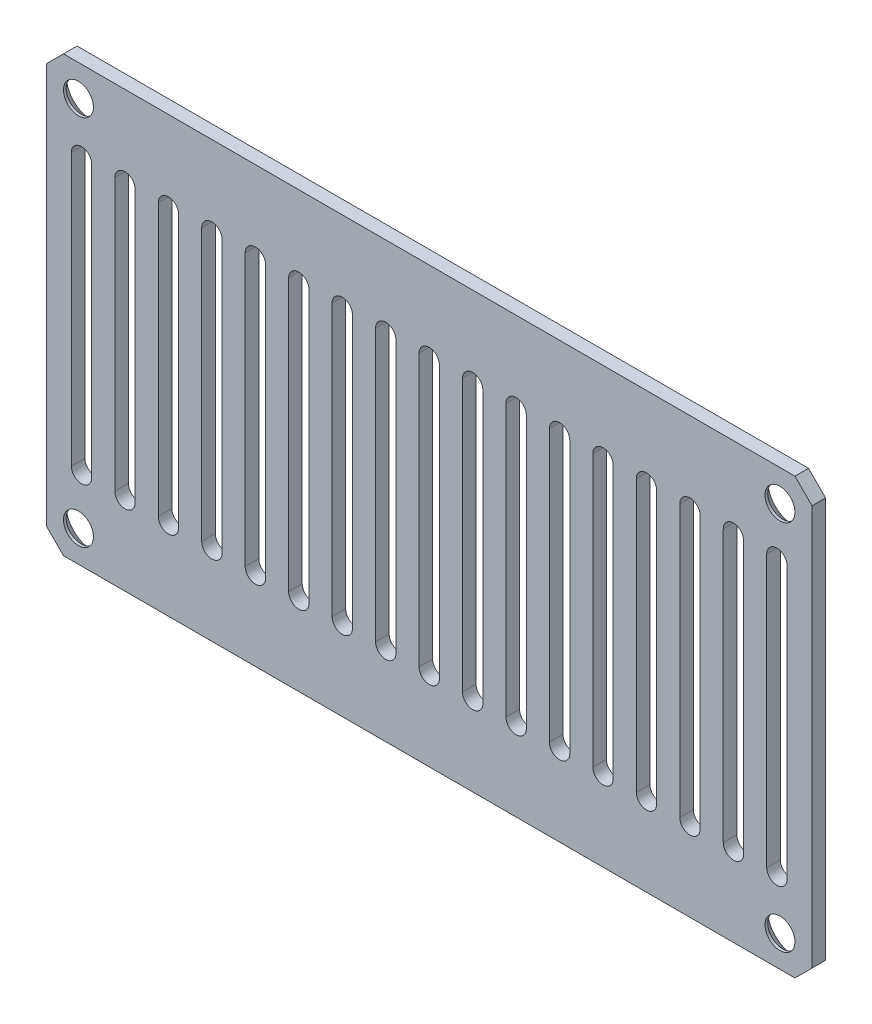
SolidWorks part; units mm, degrees
ref_plane "Front Plane" through (0, 0, 0) normal (0, 0, 1) x (1, 0, 0)
ref_plane "Top Plane" through (0, 0, 0) normal (0, 1, 0) x (1, 0, 0)
ref_plane "Right Plane" through (0, 0, 0) normal (1, 0, 0) x (0, 0, -1)
sketch "Sketch1" plane through (0, 0, 0) normal (0, 0, 1) x (1, 0, 0)
  line L1 (0, 0) -> (89.5, 0)
  line L2 (0, 0) -> (0, 50.8)
  line L3 (0, 50.8) -> (89.5, 50.8)
  line L4 (89.5, 0) -> (89.5, 50.8)
  dimension "D1" = 89.5
  dimension "D2" = 50.8
extrude "Boss-Extrude1" add sketch "Sketch1" along normal blind 1.5875
chamfer "Chamfer1" distance 2 angle 45 4 edges at (0, 0, 0.7937) (0, 50.8, 0.7937) (89.5, 0, 0.7937) (89.5, 50.8, 0.7937)
sketch "Sketch2" plane through (0, 0, 0) normal (0, 0, -1) x (-1, 0, 0)
  line L0 (-44.75, 50.8) -> (-44.75, 0) construction
  line L1 (-87.5, 50.8) -> (-2, 50.8) construction
  line L2 (-2, 0) -> (-87.5, 0) construction
  line L3 (-44.75, 41.275) -> (-44.75, 9.525) construction
  line L4 (-43.5594, 41.275) -> (-43.5594, 9.525)
  line L5 (-45.9406, 41.275) -> (-45.9406, 9.525)
  line L6 (-89.5, 25.4) -> (0, 25.4) construction
  line L7 (-89.5, 2) -> (-89.5, 48.8) construction
  line L8 (0, 48.8) -> (0, 2) construction
  line L9 (-39.67, 41.275) -> (-39.67, 9.525) construction
  line L10 (-38.4794, 41.275) -> (-38.4794, 9.525)
  line L11 (-40.8606, 41.275) -> (-40.8606, 9.525)
  line L12 (-34.59, 41.275) -> (-34.59, 9.525) construction
  line L13 (-33.3994, 41.275) -> (-33.3994, 9.525)
  line L14 (-35.7806, 41.275) -> (-35.7806, 9.525)
  line L15 (-29.51, 41.275) -> (-29.51, 9.525) construction
  line L16 (-28.3194, 41.275) -> (-28.3194, 9.525)
  line L17 (-30.7006, 41.275) -> (-30.7006, 9.525)
  line L18 (-24.43, 41.275) -> (-24.43, 9.525) construction
  line L19 (-23.2394, 41.275) -> (-23.2394, 9.525)
  line L20 (-25.6206, 41.275) -> (-25.6206, 9.525)
  line L21 (-19.35, 41.275) -> (-19.35, 9.525) construction
  line L22 (-18.1594, 41.275) -> (-18.1594, 9.525)
  line L23 (-20.5406, 41.275) -> (-20.5406, 9.525)
  line L24 (-14.27, 41.275) -> (-14.27, 9.525) construction
  line L25 (-13.0794, 41.275) -> (-13.0794, 9.525)
  line L26 (-15.4606, 41.275) -> (-15.4606, 9.525)
  line L27 (-9.19, 41.275) -> (-9.19, 9.525) construction
  line L28 (-7.9994, 41.275) -> (-7.9994, 9.525)
  line L29 (-10.3806, 41.275) -> (-10.3806, 9.525)
  line L30 (-4.11, 41.275) -> (-4.11, 9.525) construction
  line L31 (-2.9194, 41.275) -> (-2.9194, 9.525)
  line L32 (-5.3006, 41.275) -> (-5.3006, 9.525)
  line L33 (-49.83, 41.275) -> (-49.83, 9.525) construction
  line L34 (-48.6394, 41.275) -> (-48.6394, 9.525)
  line L35 (-51.0206, 41.275) -> (-51.0206, 9.525)
  line L36 (-54.91, 41.275) -> (-54.91, 9.525) construction
  line L37 (-53.7194, 41.275) -> (-53.7194, 9.525)
  line L38 (-56.1006, 41.275) -> (-56.1006, 9.525)
  line L39 (-59.99, 41.275) -> (-59.99, 9.525) construction
  line L40 (-58.7994, 41.275) -> (-58.7994, 9.525)
  line L41 (-61.1806, 41.275) -> (-61.1806, 9.525)
  line L42 (-65.07, 41.275) -> (-65.07, 9.525) construction
  line L43 (-63.8794, 41.275) -> (-63.8794, 9.525)
  line L44 (-66.2606, 41.275) -> (-66.2606, 9.525)
  line L45 (-70.15, 41.275) -> (-70.15, 9.525) construction
  line L46 (-68.9594, 41.275) -> (-68.9594, 9.525)
  line L47 (-71.3406, 41.275) -> (-71.3406, 9.525)
  line L48 (-75.23, 41.275) -> (-75.23, 9.525) construction
  line L49 (-74.0394, 41.275) -> (-74.0394, 9.525)
  line L50 (-76.4206, 41.275) -> (-76.4206, 9.525)
  line L51 (-80.31, 41.275) -> (-80.31, 9.525) construction
  line L52 (-79.1194, 41.275) -> (-79.1194, 9.525)
  line L53 (-81.5006, 41.275) -> (-81.5006, 9.525)
  line L54 (-85.39, 41.275) -> (-85.39, 9.525) construction
  line L55 (-84.1994, 41.275) -> (-84.1994, 9.525)
  line L56 (-86.5806, 41.275) -> (-86.5806, 9.525)
  arc A0 (-43.5594, 41.275) -> (-45.9406, 41.275) centre (-44.75, 41.275) ccw
  arc A1 (-45.9406, 9.525) -> (-43.5594, 9.525) centre (-44.75, 9.525) ccw
  arc A2 (-38.4794, 41.275) -> (-40.8606, 41.275) centre (-39.67, 41.275) ccw
  arc A3 (-40.8606, 9.525) -> (-38.4794, 9.525) centre (-39.67, 9.525) ccw
  arc A4 (-33.3994, 41.275) -> (-35.7806, 41.275) centre (-34.59, 41.275) ccw
  arc A5 (-35.7806, 9.525) -> (-33.3994, 9.525) centre (-34.59, 9.525) ccw
  arc A6 (-28.3194, 41.275) -> (-30.7006, 41.275) centre (-29.51, 41.275) ccw
  arc A7 (-30.7006, 9.525) -> (-28.3194, 9.525) centre (-29.51, 9.525) ccw
  arc A8 (-23.2394, 41.275) -> (-25.6206, 41.275) centre (-24.43, 41.275) ccw
  arc A9 (-25.6206, 9.525) -> (-23.2394, 9.525) centre (-24.43, 9.525) ccw
  arc A10 (-18.1594, 41.275) -> (-20.5406, 41.275) centre (-19.35, 41.275) ccw
  arc A11 (-20.5406, 9.525) -> (-18.1594, 9.525) centre (-19.35, 9.525) ccw
  arc A12 (-13.0794, 41.275) -> (-15.4606, 41.275) centre (-14.27, 41.275) ccw
  arc A13 (-15.4606, 9.525) -> (-13.0794, 9.525) centre (-14.27, 9.525) ccw
  arc A14 (-7.9994, 41.275) -> (-10.3806, 41.275) centre (-9.19, 41.275) ccw
  arc A15 (-10.3806, 9.525) -> (-7.9994, 9.525) centre (-9.19, 9.525) ccw
  arc A16 (-2.9194, 41.275) -> (-5.3006, 41.275) centre (-4.11, 41.275) ccw
  arc A17 (-5.3006, 9.525) -> (-2.9194, 9.525) centre (-4.11, 9.525) ccw
  arc A18 (-48.6394, 41.275) -> (-51.0206, 41.275) centre (-49.83, 41.275) ccw
  arc A19 (-51.0206, 9.525) -> (-48.6394, 9.525) centre (-49.83, 9.525) ccw
  arc A20 (-53.7194, 41.275) -> (-56.1006, 41.275) centre (-54.91, 41.275) ccw
  arc A21 (-56.1006, 9.525) -> (-53.7194, 9.525) centre (-54.91, 9.525) ccw
  arc A22 (-58.7994, 41.275) -> (-61.1806, 41.275) centre (-59.99, 41.275) ccw
  arc A23 (-61.1806, 9.525) -> (-58.7994, 9.525) centre (-59.99, 9.525) ccw
  arc A24 (-63.8794, 41.275) -> (-66.2606, 41.275) centre (-65.07, 41.275) ccw
  arc A25 (-66.2606, 9.525) -> (-63.8794, 9.525) centre (-65.07, 9.525) ccw
  arc A26 (-68.9594, 41.275) -> (-71.3406, 41.275) centre (-70.15, 41.275) ccw
  arc A27 (-71.3406, 9.525) -> (-68.9594, 9.525) centre (-70.15, 9.525) ccw
  arc A28 (-74.0394, 41.275) -> (-76.4206, 41.275) centre (-75.23, 41.275) ccw
  arc A29 (-76.4206, 9.525) -> (-74.0394, 9.525) centre (-75.23, 9.525) ccw
  arc A30 (-79.1194, 41.275) -> (-81.5006, 41.275) centre (-80.31, 41.275) ccw
  arc A31 (-81.5006, 9.525) -> (-79.1194, 9.525) centre (-80.31, 9.525) ccw
  arc A32 (-84.1994, 41.275) -> (-86.5806, 41.275) centre (-85.39, 41.275) ccw
  arc A33 (-86.5806, 9.525) -> (-84.1994, 9.525) centre (-85.39, 9.525) ccw
  point P8 (-44.75, 25.4)
  point P23 (-39.67, 25.4)
  point P30 (-34.59, 25.4)
  point P37 (-29.51, 25.4)
  point P44 (-24.43, 25.4)
  point P51 (-19.35, 25.4)
  point P58 (-14.27, 25.4)
  point P65 (-9.19, 25.4)
  point P72 (-4.11, 25.4)
  point P78 (-49.83, 25.4)
  point P85 (-54.91, 25.4)
  point P92 (-59.99, 25.4)
  point P99 (-65.07, 25.4)
  point P106 (-70.15, 25.4)
  point P113 (-75.23, 25.4)
  point P120 (-80.31, 25.4)
  point P127 (-85.39, 25.4)
  dimension "D1" = 2.3813
  dimension "D2" = 31.75
  dimension "D3" = 9
  dimension "D4" = 9
extrude "Cut-Extrude1" cut sketch "Sketch2" against normal through all
sketch "Sketch3" plane through (0, 0, 0) normal (0, 0, -1) x (-1, 0, 0)
  line L0 (-89.5, 25.4) -> (0, 25.4) construction
  line L1 (-89.5, 2) -> (-89.5, 48.8) construction
  line L2 (0, 48.8) -> (0, 2) construction
  line L3 (-85.75, 47.15) -> (-3.75, 47.15) construction
  line L4 (-87.5, 50.8) -> (-2, 50.8) construction
  line L5 (-44.75, 50.8) -> (-44.75, 0) construction
  line L6 (-2, 0) -> (-87.5, 0) construction
  line L7 (-3.75, 47.15) -> (-3.75, 3.65) construction
  circle A0 centre (-85.75, 47.15) radius 1.75
  circle A1 centre (-3.75, 47.15) radius 1.75
  circle A2 centre (-3.75, 3.65) radius 1.75
  circle A3 centre (-85.75, 3.65) radius 1.75
  point P20 (-44.75, 47.15)
  point P21 (-3.75, 25.4)
  dimension "D1" = 3.5
  dimension "D2" = 82
  dimension "D3" = 43.5
extrude "Cut-Extrude2" cut sketch "Sketch3" against normal through all
chamfer "Chamfer2" distance 1.27 angle 45 4 edges at (2, 3.65, 0) (84, 3.65, 0) (2, 47.15, 0) (84, 47.15, 0)
